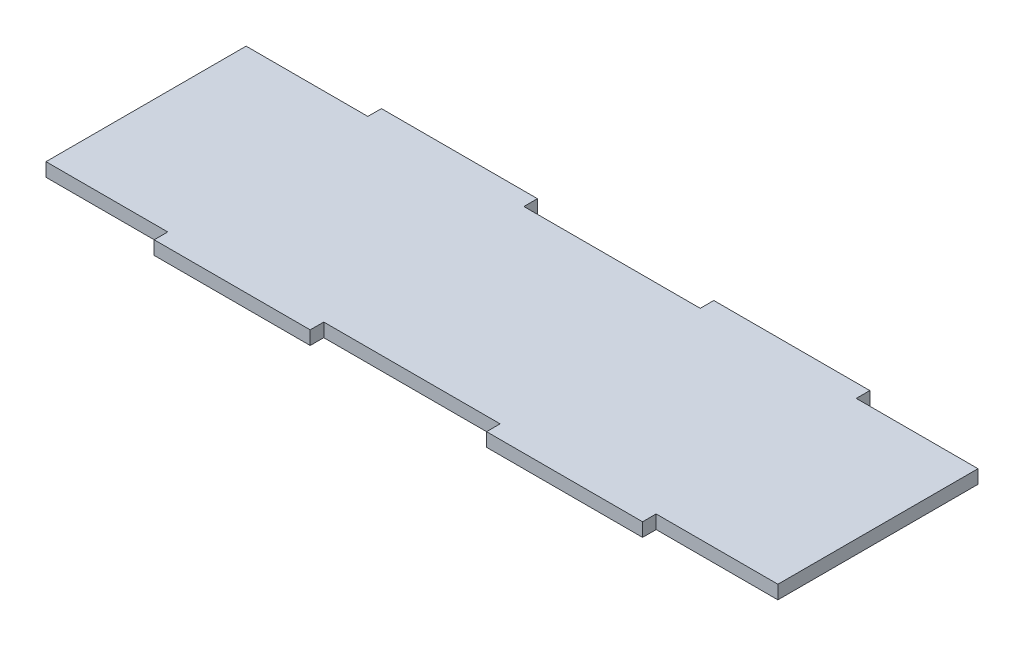
SolidWorks part; units mm, degrees
ref_plane "前视基准面" through (0, 0, 0) normal (0, 0, 1) x (1, 0, 0)
ref_plane "上视基准面" through (0, 0, 0) normal (0, 1, 0) x (1, 0, 0)
ref_plane "右视基准面" through (0, 0, 0) normal (1, 0, 0) x (0, 0, -1)
sketch "草图1" plane through (0, 0, 0) normal (0, 1, 0) x (1, 0, 0)
  line L1 (-53.95, 14.75) -> (53.95, 14.75)
  line L2 (-53.95, 14.75) -> (-53.95, -14.75)
  line L3 (-53.95, -14.75) -> (53.95, -14.75)
  line L4 (53.95, 14.75) -> (53.95, -14.75)
  line L5 (-53.95, 14.75) -> (53.95, -14.75) construction
  line L6 (-53.95, -14.75) -> (53.95, 14.75) construction
  point P0 (0, 0)
  dimension "D1" = 29.5
  dimension "D2" = 107.9
extrude "凸台-拉伸1" add sketch "草图1" along normal blind 2
sketch "草图2" plane through (0, 2, 0) normal (0, 1, 0) x (1, 0, 0)
  line L0 (53.95, 14.75) -> (-53.95, 14.75) construction
  line L1 (-36, 14.75) -> (-13, 14.75)
  line L2 (-36, 14.75) -> (-36, 16.75)
  line L3 (-36, 16.75) -> (-13, 16.75)
  line L4 (-13, 14.75) -> (-13, 16.75)
  line L7 (13, 14.75) -> (36, 14.75)
  line L8 (13, 14.75) -> (13, 16.75)
  line L9 (13, 16.75) -> (36, 16.75)
  line L10 (36, 14.75) -> (36, 16.75)
  line L11 (0, 0) -> (20.0351, 0) construction
  line L12 (36, -14.75) -> (36, -16.75)
  line L13 (13, -16.75) -> (36, -16.75)
  line L14 (13, -14.75) -> (13, -16.75)
  line L15 (13, -14.75) -> (36, -14.75)
  line L16 (-13, -14.75) -> (-13, -16.75)
  line L17 (-36, -16.75) -> (-13, -16.75)
  line L18 (-36, -14.75) -> (-36, -16.75)
  line L19 (-36, -14.75) -> (-13, -14.75)
  dimension "D1" = 13
  dimension "D2" = 23
  dimension "D3" = 2
  dimension "D4" = 2
  dimension "D5" = 13
  dimension "D6" = 23
extrude "凸台-拉伸2" add sketch "草图2" against normal blind 2
